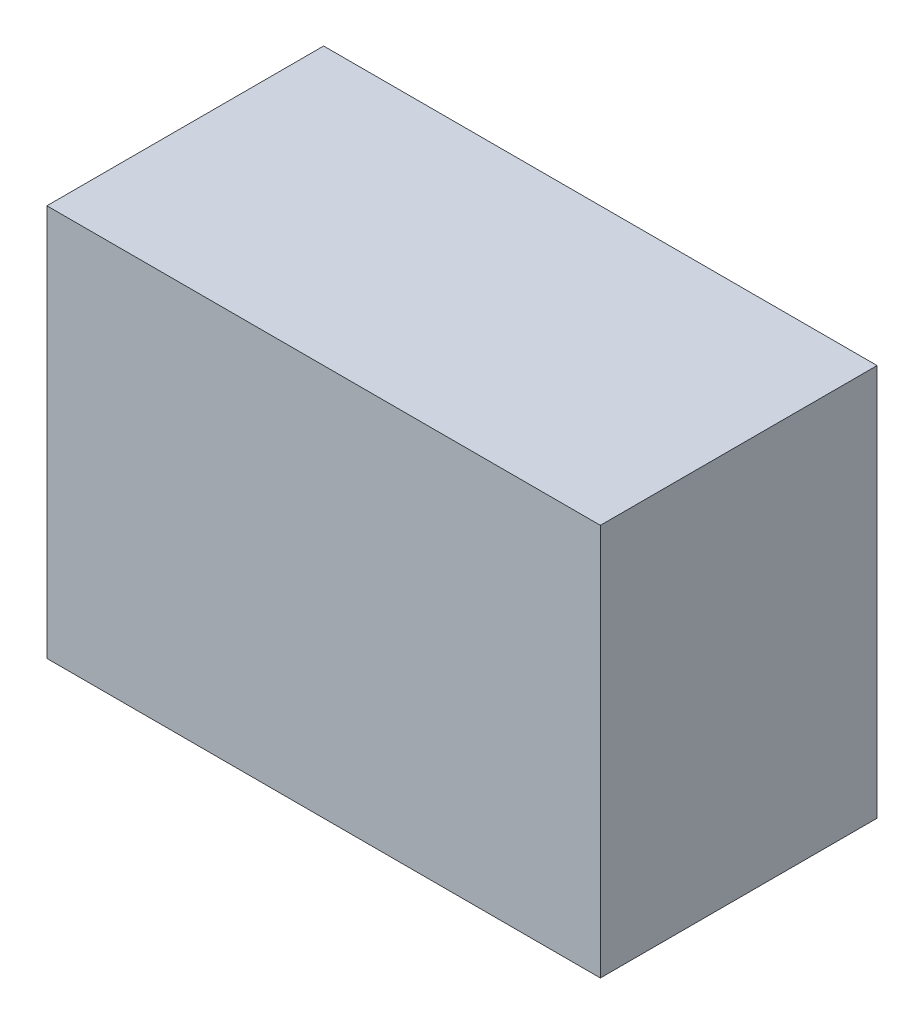
SolidWorks part; units mm, degrees
ref_plane "Front Plane" through (0, 0, 0) normal (0, 0, 1) x (1, 0, 0)
ref_plane "Top Plane" through (0, 0, 0) normal (0, 1, 0) x (1, 0, 0)
ref_plane "Right Plane" through (0, 0, 0) normal (1, 0, 0) x (0, 0, -1)
sketch "Sketch1" plane through (0, 0, 0) normal (0, 1, 0) x (1, 0, 0)
  line L1 (-24, 9.4547) -> (24, 9.4547)
  line L2 (-24, 9.4547) -> (-24, -14.5453)
  line L3 (-24, -14.5453) -> (24, -14.5453)
  line L4 (24, 9.4547) -> (24, -14.5453)
  dimension "D1" = 24
  dimension "D2" = 48
  dimension "D3" = 24
extrude "Boss-Extrude1" add sketch "Sketch1" along normal blind 34
shell "Shell1" thickness 2
sketch "Sketch2" plane through (0, 0, -9.4547) normal (0, 0, -1) x (-1, 0, 0)
  line L0 (-6.5026, 0) -> (6.5026, 0)
  line L1 (-24, 0) -> (24, 0) construction
  line L2 (6.5026, 0) -> (6.5026, 25)
  line L3 (-6.5026, 0) -> (-6.5026, 25)
  arc A1 (6.5026, 25) -> (-6.5026, 25) centre (0, 25) ccw
extrude "Cut-Extrude1" cut sketch "Sketch2" against normal blind 2
sketch "Sketch3" plane through (0, 32, 0) normal (0, -1, 0) x (1, 0, 0)
  line L0 (22, 12.5453) -> (22, -7.4547) construction
  line L1 (22, -4.5972) -> (15.5, -4.5972)
  line L2 (22, -4.5972) -> (22, 12.5453)
  line L3 (22, 12.5453) -> (15.5, 12.5453)
  line L4 (15.5, -4.5972) -> (15.5, 12.5453)
  line L5 (-22, 12.5453) -> (22, 12.5453) construction
  line L6 (-22, -7.4547) -> (-22, 12.5453) construction
  line L7 (-22, -4.5972) -> (-15.5, -4.5972)
  line L8 (-22, -4.5972) -> (-22, 12.5453)
  line L9 (-22, 12.5453) -> (-15.5, 12.5453)
  line L10 (-15.5, -4.5972) -> (-15.5, 12.5453)
  dimension "D1" = 6.5
  dimension "D2" = 6.5
extrude "Boss-Extrude2" add sketch "Sketch3" along normal up to surface (32 mm away) up to face at (0, 0, -1.1214)
sketch "Sketch4" plane through (0, 0, 0) normal (0, -1, 0) x (1, 0, 0)
  line L0 (24, 14.5453) -> (24, -9.4547) construction
  line L1 (-24, -9.4547) -> (-24, 14.5453) construction
  line L2 (-24, 14.5453) -> (24, 14.5453) construction
  circle A0 centre (20, 5.5453) radius 1.75
  circle A1 centre (-20, 5.5453) radius 1.75
  dimension "D1" = 4
  dimension "D2" = 4
  dimension "D3" = 9
  dimension "D4" = 9
extrude "Cut-Extrude2" cut sketch "Sketch4" against normal blind 10
